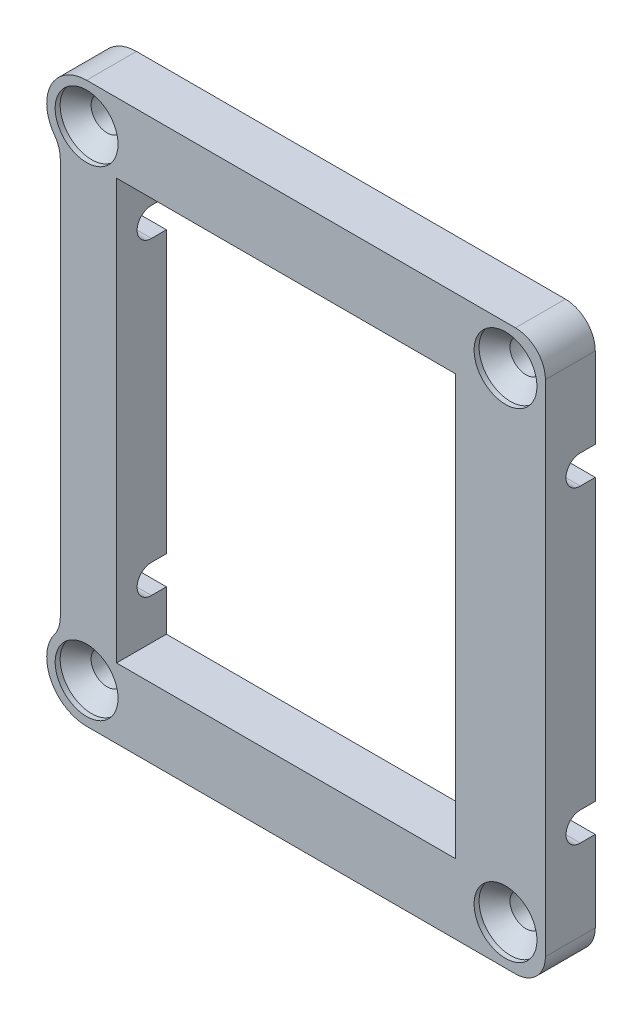
SolidWorks part; units mm, degrees
material "ABS"
ref_plane "Front Plane" through (0, 0, 0) normal (0, 0, 1) x (1, 0, 0)
ref_plane "Top Plane" through (0, 0, 0) normal (0, 1, 0) x (1, 0, 0)
ref_plane "Right Plane" through (0, 0, 0) normal (1, 0, 0) x (0, 0, -1)
sketch "Sketch1" plane through (0, 0, 0) normal (0, 0, 1) x (1, 0, 0)
  line L0 (23.0539, -73.6389) -> (23.0539, -115.7389)
  line L1 (20.0539, -66.6389) -> (63.0539, -66.6389)
  line L2 (17.4139, -73.644) -> (17.4139, -115.7339)
  line L3 (20.0539, -122.7389) -> (63.0539, -122.7389)
  line L4 (66.0539, -69.6389) -> (66.0539, -119.7389)
  line L10 (23.0539, -115.7389) -> (59.0539, -115.7389)
  line L12 (59.0539, -73.6389) -> (59.0539, -115.7389)
  line L13 (59.0539, -73.6389) -> (23.0539, -73.6389)
  line L15 (66.0539, -101.9889) -> (66.0539, -117.3889) construction
  line L17 (17.4139, -89.1889) -> (17.4139, -76.6389) construction
  arc A0 (63.0539, -66.6389) -> (66.0539, -69.6389) centre (63.0539, -69.6389) cw
  arc A3 (63.0539, -122.7389) -> (66.0539, -119.7389) centre (63.0539, -119.7389) ccw
  circle A4 centre (20.0539, -70.6389) radius 1.25
  circle A5 centre (20.0539, -118.7389) radius 1.25
  circle A6 centre (62.0539, -70.6389) radius 1.25
  circle A7 centre (62.0539, -118.7389) radius 1.25
  arc A8 (20.0539, -66.6389) -> (17.4139, -73.644) centre (20.0539, -70.6389) ccw
  arc A9 (17.4139, -115.7339) -> (20.0539, -122.7389) centre (20.0539, -118.7389) ccw
  dimension "D3" = 3
  dimension "D1" = 7
  dimension "D2" = 7
extrude "Boss-Extrude1" add sketch "Sketch1" along normal blind 5
sketch "Sketch6" plane through (0, 0, 5) normal (0, 0, 1) x (1, 0, 0)
  line L0 (59.0539, -73.6389) -> (23.0539, -73.6389) construction
  line L1 (59.0539, -115.7389) -> (57.0539, -115.7389)
  line L2 (59.0539, -115.7389) -> (59.0539, -73.6389)
  line L3 (59.0539, -73.6389) -> (57.0539, -73.6389)
  line L4 (57.0539, -115.7389) -> (57.0539, -73.6389)
extrude "Boss-Extrude4" add sketch "Sketch6" against normal up to vertex (5 mm away)
hole_wizard "CSK for M3 Countersunk Flat Head Screw1" positions "Sketch3" profile "Sketch2" countersink size "M3" standard "ISO" end condition through all
sketch "Sketch3" plane through (0, 0, 5) normal (0, 0, 1) x (1, 0, 0)
  point P0 (20.0539, -118.7389)
  point P2 (20.0539, -70.6389)
  point P4 (62.0539, -70.6389)
  point P6 (62.0539, -118.7389)
sketch "Sketch2" plane through (20.0539, -118.7389, 5) normal (1, 0, 0) x (0, -1, 0)
  line L0 (0, 0) -> (0, 5)
  line L1 (0, 5) -> (1.6, 5)
  line L2 (1.6, 5) -> (1.6, 2.05)
  line L3 (1.6, 2.05) -> (3.15, 0.5)
  line L4 (3.15, 0.5) -> (3.15, 0)
  line L6 (3.15, 0) -> (0, 0)
  line L7 (-1.6, 2.05) -> (-3.15, 0.5) construction
  line L11 (0, -6.35) -> (0, 107.95) construction
  dimension "Thru Hole Dia." = 3.2
  dimension "Thru Hole Depth" = 5
  dimension "C'Sink Dia." = 6.3
  dimension "C'Sink Angle" = 90
  dimension "Head Clearance" = 0.5
hole_wizard "Furo com folga de M34" positions "Sketch5" profile "Sketch4" hole size "M3" standard "Ansi Metric" end condition through all
sketch "Sketch5" plane through (66.0539, 0, 0) normal (1, 0, 0) x (0, 0, -1)
  circle A1 centre (-1.5, -110.1889) radius 1.5
  circle A3 centre (-1.5, -79.1889) radius 1.5
  point P0 (-1.5, -79.1889)
  point P2 (-1.5, -110.1889)
sketch "Sketch4" plane through (66.0539, -79.1889, 1.5) normal (0, 1, 0) x (0, 0, -1)
  line L0 (0, 0) -> (0, 50)
  line L1 (0, 50) -> (1.435, 50)
  line L2 (1.435, 50) -> (1.435, 0)
  line L5 (1.435, 0) -> (0, 0)
  line L11 (0, -6.35) -> (0, 107.95) construction
  dimension "Thru Hole Dia." = 2.87
  dimension "Thru Hole Depth" = 50
fillet "Filete1" radius 3 2 edges at (17.4139, -115.7339, 2.5) (17.4139, -73.644, 2.5)
sketch "Esboço3" plane through (57.0539, 0, 0) normal (-1, 0, 0) x (0, 0, 1)
  line L1 (1.5, -80.6239) -> (0, -80.6239)
  line L2 (1.5, -80.6239) -> (1.5, -77.7539)
  line L3 (1.5, -77.7539) -> (0, -77.7539)
  line L4 (0, -80.6239) -> (0, -77.7539)
  line L5 (0, -73.6389) -> (0, -115.7389) construction
  line L6 (1.5, -108.7539) -> (0, -108.7539)
  line L7 (1.5, -108.7539) -> (1.5, -111.6239)
  line L8 (1.5, -111.6239) -> (0, -111.6239)
  line L9 (0, -108.7539) -> (0, -111.6239)
  circle A0 centre (1.5, -79.1889) radius 1.435 construction
  circle A1 centre (1.5, -110.1889) radius 1.435 construction
  circle A4 centre (1.5, -110.1889) radius 1.435 construction
extrude "Corte-extrusão1" cut sketch "Esboço3" along normal blind 63 and the other way blind 10
